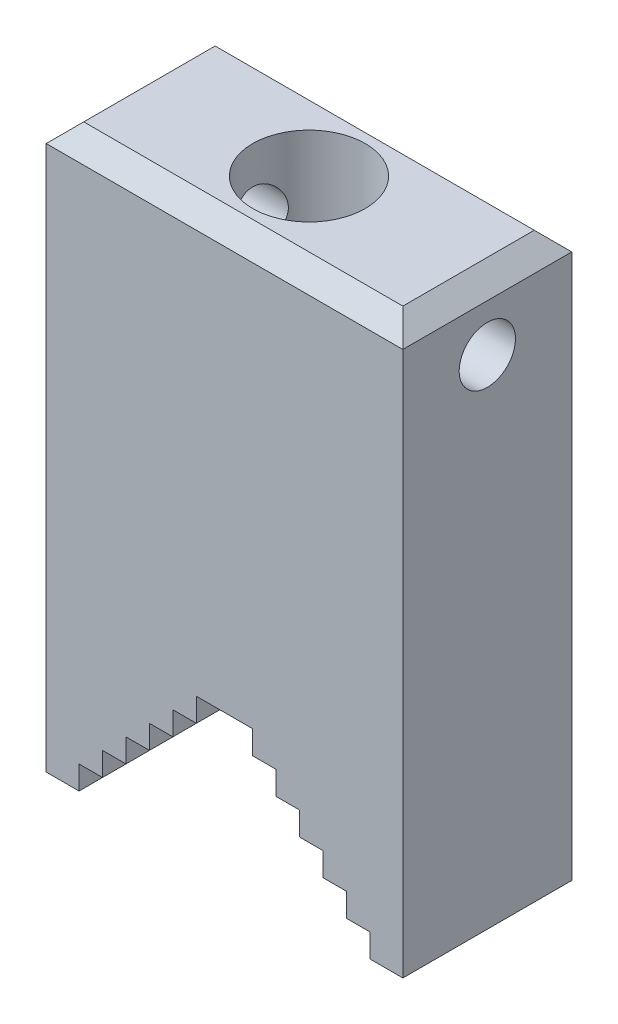
SolidWorks part; units mm, degrees
ref_plane "Front Plane" through (0, 0, 0) normal (0, 0, 1) x (1, 0, 0)
ref_plane "Top Plane" through (0, 0, 0) normal (0, 1, 0) x (1, 0, 0)
ref_plane "Right Plane" through (0, 0, 0) normal (1, 0, 0) x (0, 0, -1)
sketch "Sketch1" plane through (0, 0, 0) normal (0, 0, 1) x (1, 0, 0)
  line L0 (0, 95.7651) -> (0, -35.3361) construction
  line L1 (-19, 0) -> (-19, 60)
  line L2 (-19, 60) -> (19, 60)
  line L3 (19, 0) -> (19, 60)
  line L4 (-19, 0) -> (19, 0)
  point P7 (0, 0)
  point P9 (0, 60)
  dimension "D1" = 60
  dimension "D2" = 19
extrude "Boss-Extrude1" add sketch "Sketch1" along normal mid plane 18
sketch "Sketch2" plane through (0, 0, 9) normal (0, 0, 1) x (1, 0, 0)
  line L0 (0, 65.658) -> (0, -1.9712) construction
  line L1 (-15.5, 0) -> (-15.5, 2.5)
  line L2 (-19, 0) -> (19, 0) construction
  line L3 (-15.5, 2.5) -> (-13, 2.5)
  line L4 (-13, 2.5) -> (-13, 5)
  line L5 (-13, 5) -> (-10.5, 5)
  line L6 (-10.5, 5) -> (-10.5, 7.5)
  line L7 (-10.5, 7.5) -> (-8, 7.5)
  line L8 (-8, 7.5) -> (-8, 10)
  line L9 (-8, 10) -> (-5.5, 10)
  line L10 (-5.5, 10) -> (-5.5, 12.5)
  line L11 (-5.5, 12.5) -> (-3, 12.5)
  line L12 (-3, 12.5) -> (-3, 15)
  line L13 (3, 12.5) -> (3, 15)
  line L14 (5.5, 12.5) -> (3, 12.5)
  line L15 (5.5, 10) -> (5.5, 12.5)
  line L16 (8, 10) -> (5.5, 10)
  line L17 (8, 7.5) -> (8, 10)
  line L18 (10.5, 7.5) -> (8, 7.5)
  line L19 (10.5, 5) -> (10.5, 7.5)
  line L20 (13, 5) -> (10.5, 5)
  line L21 (13, 2.5) -> (13, 5)
  line L22 (15.5, 2.5) -> (13, 2.5)
  line L23 (15.5, 0) -> (15.5, 2.5)
  line L24 (-3, 15) -> (3, 15)
  line L25 (-19, 60) -> (-19, 0) construction
  line L26 (19, 0) -> (19, 60) construction
  dimension "D1" = 3.5
  dimension "D2" = 2.5
  dimension "D3" = 2.5
  dimension "D4" = 2.5
  dimension "D5" = 2.5
  dimension "D6" = 2.5
  dimension "D7" = 2.5
  dimension "D8" = 2.5
  dimension "D9" = 2.5
  dimension "D10" = 2.5
  dimension "D11" = 2.5
  dimension "D12" = 2.5
extrude "Cut-Extrude1" cut sketch "Sketch2" against normal blind 18 and the other way through all
sketch "Sketch4" plane through (0, 0, 0) normal (0, 0, 1) x (1, 0, 0)
  line L0 (0, 73.0718) -> (0, 0) construction
  line L1 (-6, 60) -> (-6, 40)
  line L2 (19, 60) -> (-19, 60) construction
  line L3 (-6, 40) -> (0, 36.5359)
  line L4 (-6, 40) -> (0, 40) construction
  line L5 (-6, 60) -> (0, 60)
  line L6 (0, 60) -> (0, 36.5359)
  dimension "D1" = 6
  dimension "D2" = 60
  dimension "D3" = 20
revolve "Cut-Revolve1" cut sketch "Sketch4" angle 360 about L0
sketch "Sketch5" plane through (19, 0, 0) normal (1, 0, 0) x (0, 0, -1)
  line L0 (-9, 60) -> (9, 60) construction
  line L1 (0, 64.8053) -> (0, 0) construction
  line L2 (9, 0) -> (9, 60) construction
  circle A0 centre (0, 53) radius 3
  dimension "D1" = 6
  dimension "D2" = 7
  dimension "D3" = 9
extrude "Cut-Extrude2" cut sketch "Sketch5" against normal up to surface (38 mm away) up to face at (-19, 30, 0)
chamfer "Chamfer1" distance 2 angle 45 4 edges at (0, 60, -9) (-19, 60, 0) (19, 60, 0) (0, 60, 9)
